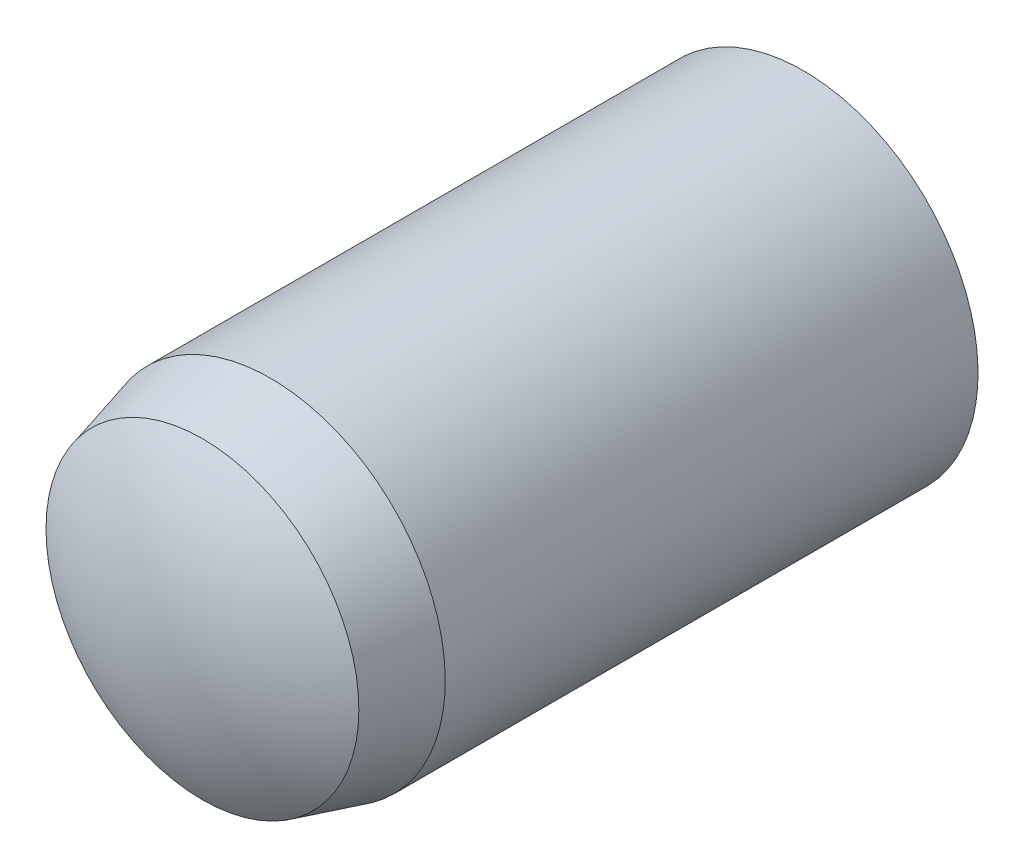
SolidWorks part; units mm, degrees
ref_plane "Front Plane" through (0, 0, 0) normal (0, 0, 1) x (1, 0, 0)
ref_plane "Top Plane" through (0, 0, 0) normal (0, 1, 0) x (1, 0, 0)
ref_plane "Right Plane" through (0, 0, 0) normal (1, 0, 0) x (0, 0, -1)
sketch "Sketch1" plane through (0, 0, 0) normal (0, 0, 1) x (1, 0, 0)
  circle A0 centre (0, 0) radius 1.5
  point P3 (0, 1.5)
  dimension "Diameter" = 3
sketch "Sketch2" plane through (0, 0, 0) normal (1, 0, 0) x (0, 0, -1)
  line L0 (-3, 0) -> (3, 0) construction
  line L1 (-3, 0) -> (-3, 1.5) construction
  line L2 (-3, 1.5) -> (3, 1.5)
  line L3 (3, 1.5) -> (3, 0) construction
  line L4 (-2.61, 1.3432) -> (-2.025, 1.5)
  arc A0 (-3, 0) -> (-2.61, 1.3432) centre (-0.4918, 0) cw
  arc A1 (3, 0) -> (2.55, 1.5) centre (0.275, 0) ccw
  point P2 (0, 0)
  point P11 (0, 0)
  point P13 (0, 0)
  dimension "Length" = 6
  dimension "D1" = 15
  dimension "D2" = 0.45
  dimension "D3" = 0.975
  dimension "D4" = 0.585
  dimension "D5" = 3
  dimension "D6" = 3
sketch "Sketch3" plane through (0, 0, 0) normal (1, 0, 0) x (0, 0, -1)
  line L0 (-3, 0) -> (3, 0) construction
  line L1 (-2.61, 1.3432) -> (-2.025, 1.5) construction
  line L2 (-3, 0) -> (3, 0)
  line L3 (-2.61, 1.3432) -> (-2.025, 1.5)
  line L4 (-2.025, 1.5) -> (2.55, 1.5)
  arc A0 (3, 0) -> (2.55, 1.5) centre (0.275, 0) ccw construction
  arc A1 (-2.61, 1.3432) -> (-3, 0) centre (-0.4918, 0) ccw construction
  arc A2 (3, 0) -> (2.55, 1.5) centre (0.275, 0) ccw
  arc A3 (-2.61, 1.3432) -> (-3, 0) centre (-0.4918, 0) ccw
revolve "Revolve1" add sketch "Sketch3" angle 360 about L2
equation "\"D2@Sketch2\" = \"Diameter@Sketch1\" * .15"
equation "\"D3@Sketch2\" = \"Diameter@Sketch1\" * .325"
equation "\"D4@Sketch2\" = \"D3@Sketch2\" * .6"
equation "\"D5@Sketch2\"=\"Diameter@Sketch1\""
equation "\"D6@Sketch2\"=\"D5@sketch2\""
